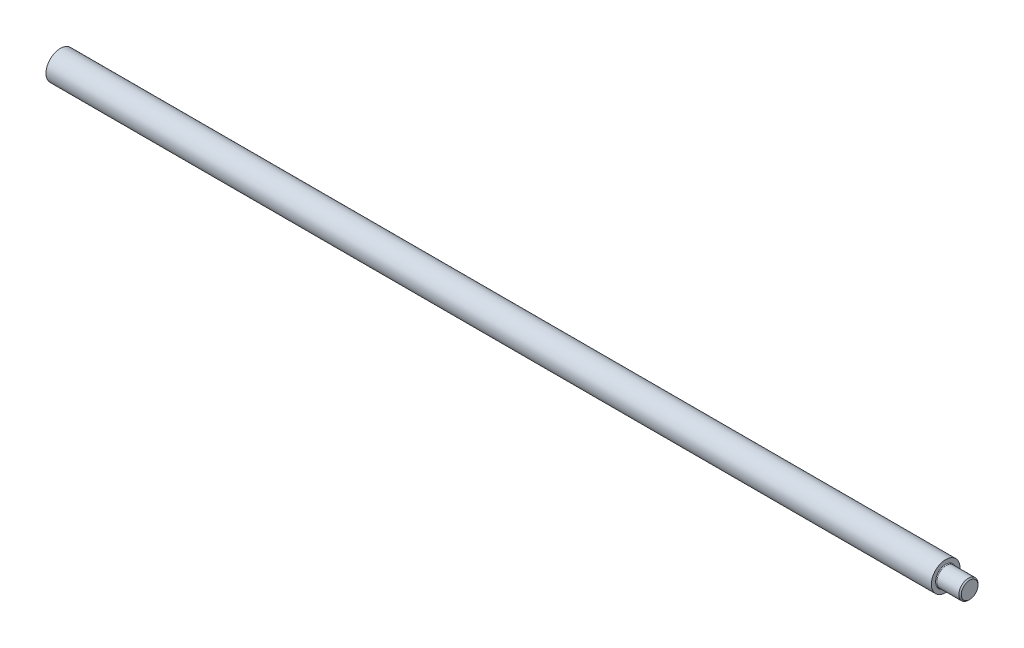
SolidWorks part; units mm, degrees
ref_plane "Piano frontale" through (0, 0, 0) normal (0, 0, 1) x (1, 0, 0)
ref_plane "Piano superiore" through (0, 0, 0) normal (0, 1, 0) x (1, 0, 0)
ref_plane "Piano destro" through (0, 0, 0) normal (1, 0, 0) x (0, 0, -1)
sketch "Sketch1" plane through (0, 0, 0) normal (0, 0, 1) x (1, 0, 0)
  line L0 (0, 6) -> (0, 0)
  line L1 (0, 0) -> (380, 0)
  line L2 (380, 0) -> (380, 3.5)
  line L3 (380, 3.5) -> (379.5, 4)
  line L4 (379.5, 4) -> (370.3, 4)
  line L5 (370, 4.3) -> (370, 6)
  line L6 (370, 6) -> (0, 6)
  line L7 (0, 0) -> (380, 0) construction
  arc A0 (370.3, 4) -> (370, 4.3) centre (370.3, 4.3) cw
revolve "Revolve1" add sketch "Sketch1" angle 360 about L7
